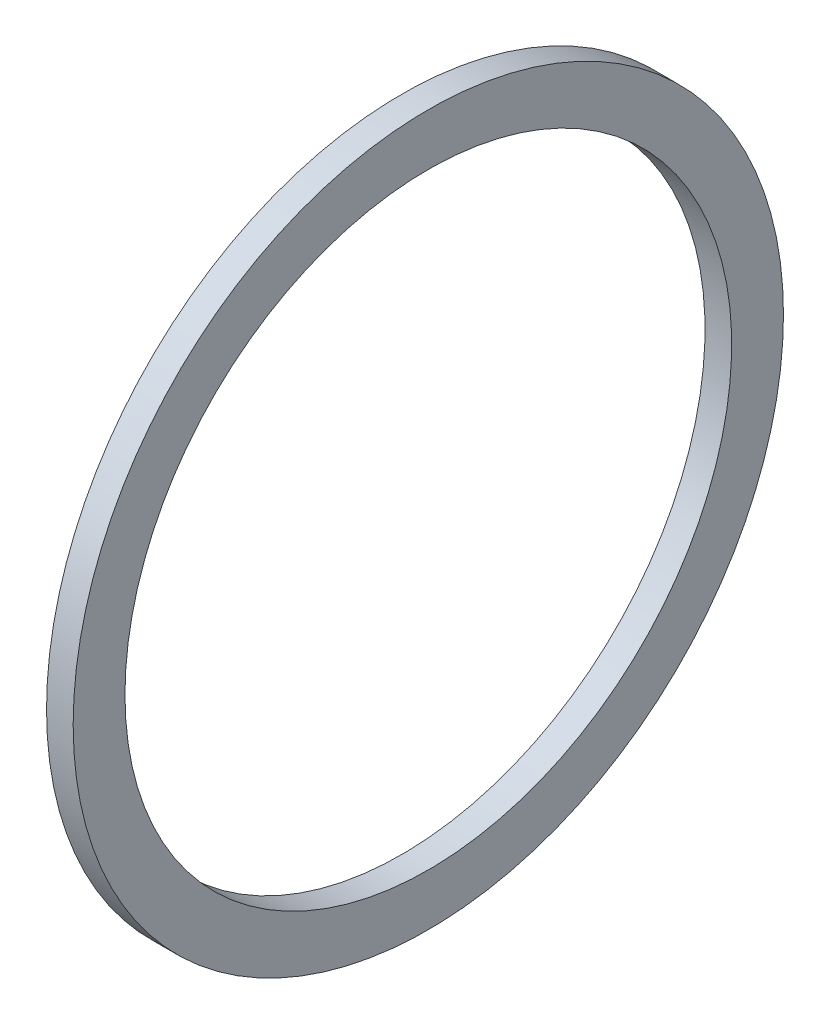
SolidWorks part; units mm, degrees
ref_plane "Front Plane" through (0, 0, 0) normal (0, 0, 1) x (1, 0, 0)
ref_plane "Top Plane" through (0, 0, 0) normal (0, 1, 0) x (1, 0, 0)
ref_plane "Right Plane" through (0, 0, 0) normal (1, 0, 0) x (0, 0, -1)
sketch "Sketch1" plane through (0, 0, 0) normal (0, 0, 1) x (1, 0, 0)
  line L0 (0, 111.25) -> (0, 0) construction
  line L1 (0, 0) -> (81.6598, 0) construction
  line L3 (-4.5, 102.5) -> (4.5, 102.5)
  line L4 (-4.5, 102.5) -> (-4.5, 120)
  line L5 (-4.5, 120) -> (4.5, 120)
  line L6 (4.5, 102.5) -> (4.5, 120)
  line L7 (-4.5, 102.5) -> (4.5, 120) construction
  line L8 (-4.5, 120) -> (4.5, 102.5) construction
  dimension "D1" = 102.5
  dimension "D2" = 120
  dimension "D3" = 9
revolve "Revolve1" add sketch "Sketch1" angle 360 about L1
